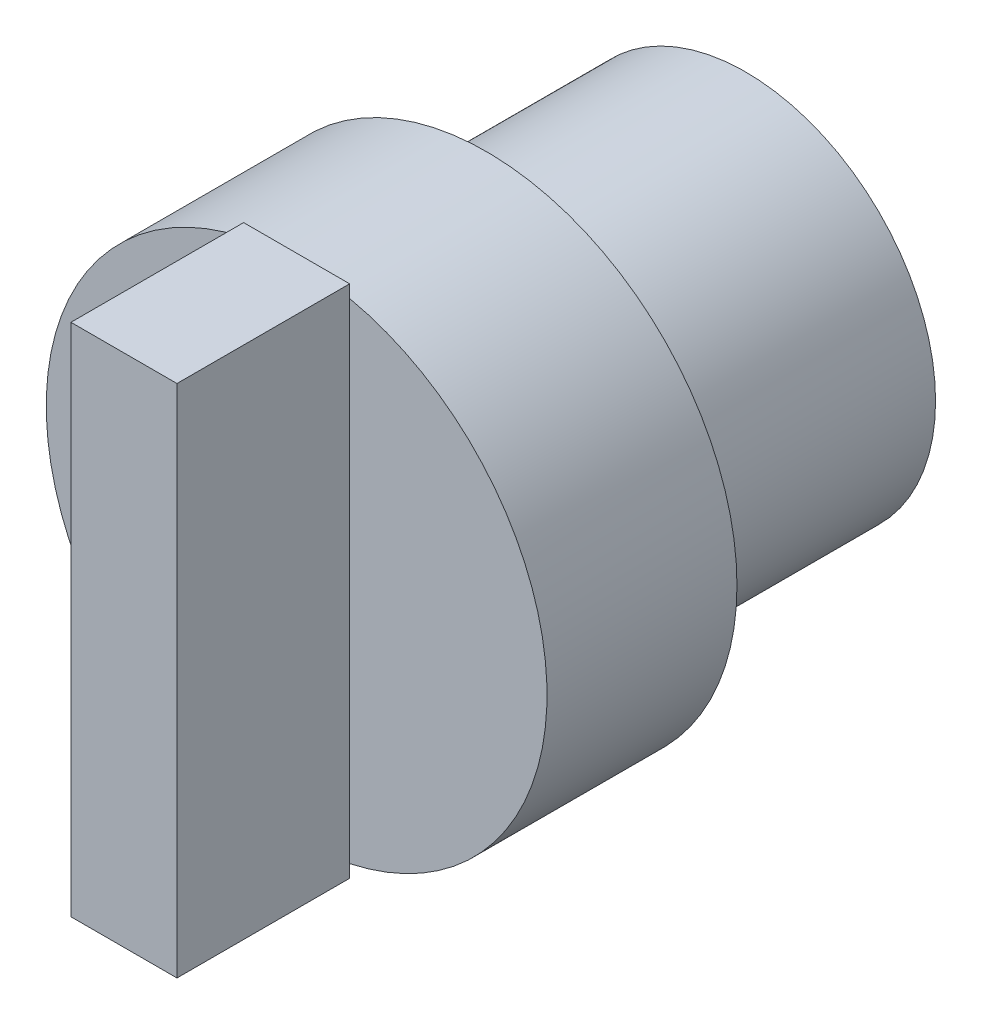
SolidWorks part; units mm, degrees
ref_plane "前视基准面" through (0, 0, 0) normal (0, 0, 1) x (1, 0, 0)
ref_plane "上视基准面" through (0, 0, 0) normal (0, 1, 0) x (1, 0, 0)
ref_plane "右视基准面" through (0, 0, 0) normal (1, 0, 0) x (0, 0, -1)
sketch "草图1" plane through (0, 0, 0) normal (0, 0, 1) x (1, 0, 0)
  circle A0 centre (0, 0) radius 11
extrude "凸台-拉伸1" add sketch "草图1" along normal blind 15
sketch "草图2" plane through (0, 0, 15) normal (0, 0, 1) x (1, 0, 0)
  circle A0 centre (0, 0) radius 14.5
extrude "凸台-拉伸2" add sketch "草图2" along normal blind 11
sketch "草图3" plane through (0, 0, 26) normal (0, 0, 1) x (1, 0, 0)
  line L1 (3.0702, 14.9073) -> (-3.0702, 14.9073)
  line L2 (3.0702, 14.9073) -> (3.0702, -14.9073)
  line L3 (3.0702, -14.9073) -> (-3.0702, -14.9073)
  line L4 (-3.0702, 14.9073) -> (-3.0702, -14.9073)
  line L5 (3.0702, 14.9073) -> (-3.0702, -14.9073) construction
  line L6 (3.0702, -14.9073) -> (-3.0702, 14.9073) construction
  point P0 (0, 0)
extrude "凸台-拉伸3" add sketch "草图3" along normal blind 10
